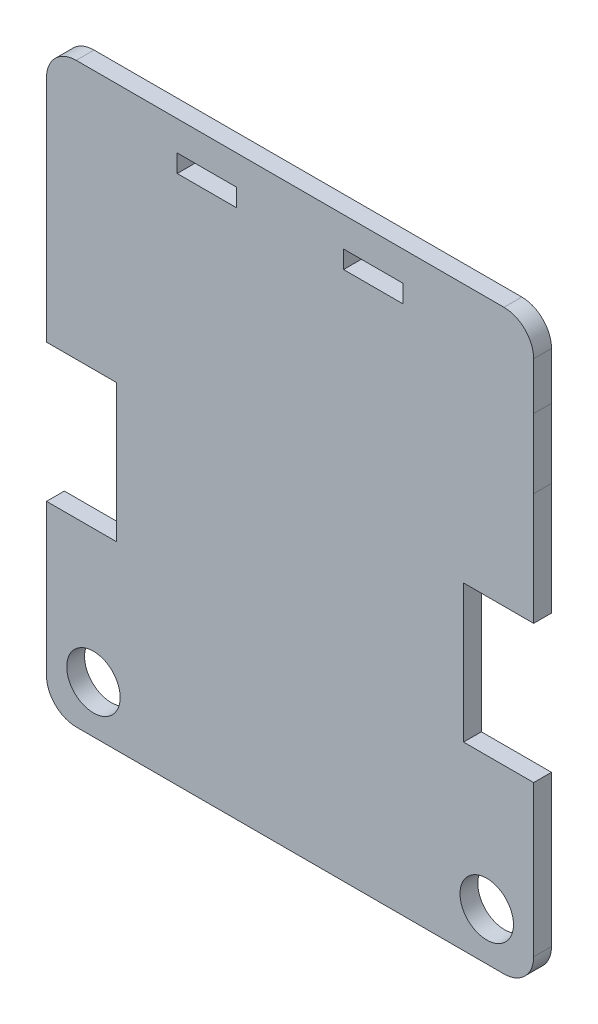
SolidWorks part; units mm, degrees
ref_plane "Alzado" through (0, 0, 0) normal (0, 0, 1) x (1, 0, 0)
ref_plane "Planta" through (0, 0, 0) normal (0, 1, 0) x (1, 0, 0)
ref_plane "Vista lateral" through (0, 0, 0) normal (1, 0, 0) x (0, 0, -1)
sketch "Model" plane through (0, 0, 0) normal (0, 0, 1) x (1, 0, 0)
  line L0 (17.8319, 53.6883) -> (41.9441, 53.6883)
  line L1 (41.9441, 53.6883) -> (62.6865, 53.6883)
  line L2 (77.2035, 19.5507) -> (77.2035, 10.1046)
  line L3 (77.2035, 29.0099) -> (77.2035, 19.5507)
  line L4 (77.2035, -33.1904) -> (77.2035, -13.0954)
  line L5 (77.2005, 40.6883) -> (77.2035, 48.6883)
  line L6 (77.2035, 29.0099) -> (77.2005, 40.6883)
  line L7 (0.2066, -43.4954) -> (72.2035, -43.4954)
  line L8 (-4.7934, -13.0954) -> (-4.7934, -38.4954)
  line L10 (77.2035, -38.4954) -> (77.2035, -33.1904)
  line L11 (17.2035, 48.6883) -> (17.2035, 45.6883)
  line L12 (27.2035, 48.6883) -> (17.2035, 48.6883)
  line L13 (27.2035, 45.6883) -> (27.2035, 48.6883)
  line L14 (17.2035, 45.6883) -> (27.2035, 45.6883)
  line L15 (55.2035, 48.6883) -> (45.2035, 48.6883)
  line L16 (55.2035, 45.6883) -> (55.2035, 48.6883)
  line L17 (45.2035, 45.6883) -> (55.2035, 45.6883)
  line L18 (45.2035, 48.6883) -> (45.2035, 45.6883)
  line L19 (7.0066, 10.1046) -> (-4.7934, 10.1046)
  line L20 (7.0066, -13.0954) -> (7.0066, 10.1046)
  line L21 (-4.7934, -13.0954) -> (7.0066, -13.0954)
  line L22 (-4.7934, 40.6883) -> (-4.7934, 10.1046)
  line L23 (-4.7934, 48.6883) -> (-4.7934, 40.6883)
  line L24 (6.6815, 53.6883) -> (0.2066, 53.6883)
  line L25 (65.4035, -13.0954) -> (77.2035, -13.0954)
  line L26 (65.4035, 10.1046) -> (65.4035, -13.0954)
  line L27 (77.2035, 10.1046) -> (65.4035, 10.1046)
  line L28 (6.6815, 53.6883) -> (17.8319, 53.6883)
  line L29 (62.6865, 53.6883) -> (72.2035, 53.6883)
  circle A0 centre (69.3035, -35.4954) radius 4.5
  circle A1 centre (3.1035, -35.4954) radius 4.5
  arc A2 (77.2035, 48.6883) -> (72.2035, 53.6883) centre (72.2035, 48.6883) ccw
  arc A3 (-4.7934, -38.4954) -> (0.2066, -43.4954) centre (0.2066, -38.4954) ccw
  arc A4 (72.2035, -43.4954) -> (77.2035, -38.4954) centre (72.2035, -38.4954) ccw
  arc A5 (0.2066, 53.6883) -> (-4.7934, 48.6883) centre (0.2066, 48.6883) ccw
extrude "Saliente-Extruir1" add sketch "Model" along normal blind 3
